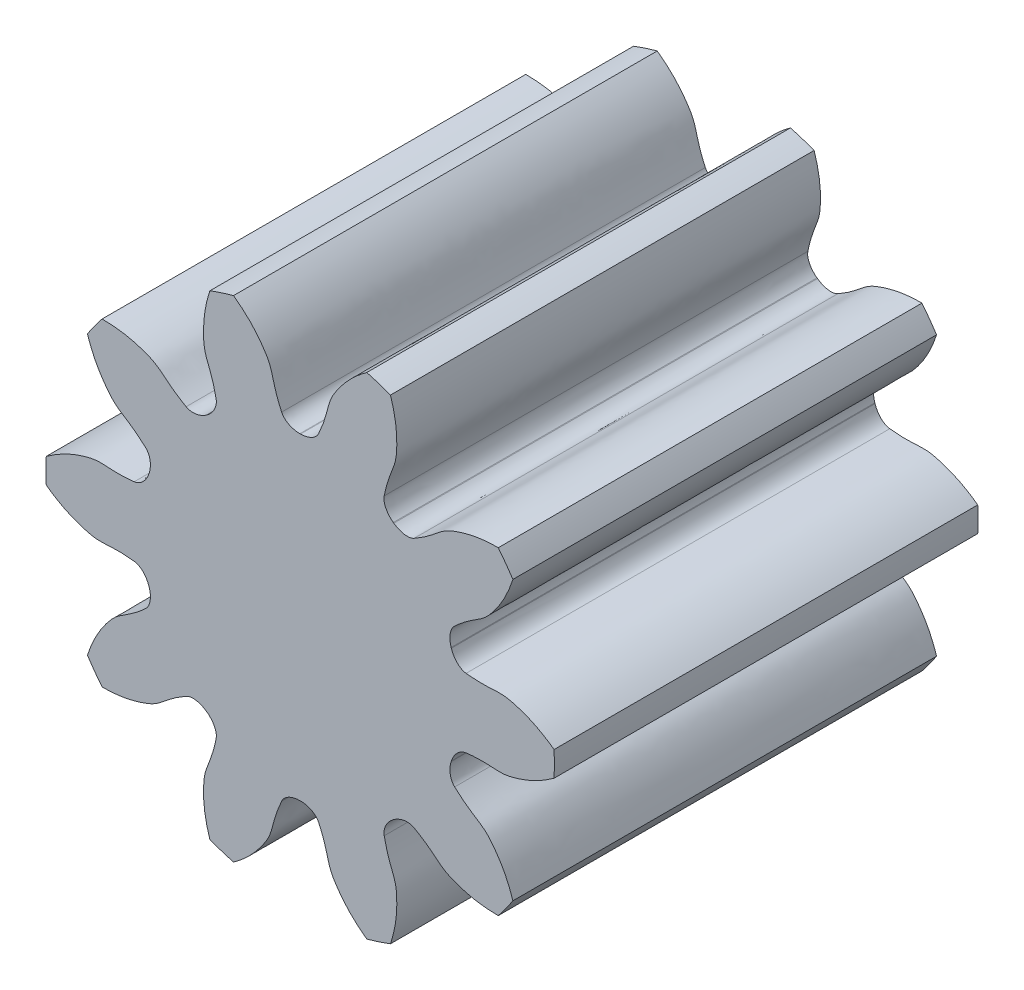
SolidWorks part; units mm, degrees
ref_plane "Plan de face" through (0, 0, 0) normal (0, 0, 1) x (1, 0, 0)
ref_plane "Plan de dessus" through (0, 0, 0) normal (0, 1, 0) x (1, 0, 0)
ref_plane "Plan de droite" through (0, 0, 0) normal (1, 0, 0) x (0, 0, -1)
sketch "Esquisse1" plane through (0, 0, 0) normal (0, 0, 1) x (1, 0, 0)
  circle A0 centre (0, 0) radius 2.4
  dimension "D1" = 4.8
extrude "Boss.-Extru.1" add sketch "Esquisse1" along normal blind 4
sketch "Dépose" plane through (-0.0454, -0.0909, 4) normal (0, 0, 1) x (1, 0, 0)
  line L0 (0.0454, 0.0909) -> (0.0454, 2.4909) construction
  circle A0 centre (0.0454, 0.0909) radius 2.4
  circle A1 centre (0.0454, 0.0909) radius 2.4 construction
  dimension "(d arbre)" = 4.8
sketch "Dimensions" plane through (-0.0454, -2.6509, 4) normal (0, 0, 1) x (1, 0, 0)
  line L0 (0.0454, 2.6509) -> (2.4454, 2.6509) construction
  line L1 (0.0454, 2.6509) -> (0.0454, 12.6509) construction
  line L2 (0.0454, 5.0509) -> (0.0454, 5.4509) construction
  line L3 (0.0454, 5.4509) -> (0.0454, 6.4509) construction
  line L4 (0.0454, 2.6509) -> (0.0454, 5.0509) construction
  line L5 (0.0454, 2.6509) -> (0.9851, 2.3088) construction
  line L6 (0.9851, 2.3088) -> (1.3387, 1.9553) construction
  line L7 (1.3387, 1.9553) -> (1.6922, 1.6017) construction
  line L8 (1.6922, 1.6017) -> (1.6993, 1.5947) construction
  line L9 (1.6993, 1.5947) -> (2.3357, 0.9583) construction
  line L10 (0.0454, 2.6509) -> (0.0454, 5.0509) construction
  line L11 (0.0454, 2.6509) -> (-0.9546, 2.6509) construction
  circle A0 centre (0.0454, 2.6509) radius 2.4 construction
  circle A1 centre (0.0454, 2.6509) radius 2.4
  circle A3 centre (0.0454, 5.2509) radius 0.2 construction
  circle A4 centre (0.0454, 2.6509) radius 2.4 construction
  dimension "(d tête)" = 4.8
  dimension "Z nb de dents" = 10
  dimension "module" = 0.4
  dimension "déport X+1" = 1
  dimension "A° de pression" = 20
  dimension "coef courbure flanc" = 1
  dimension "coef courbure raccord flanc" = 0.5
  dimension "coef courbure raccord fond" = 0.5
  dimension "coef fond/creux" = 0.01
  dimension "coef décalage bas-flanc" = 0.9
  dimension "A° tangence bas-flanc" = 25
  dimension "Reconstructions" = 1
ref_plane "Normal" through (0, 0, 4) normal (0, 0, 1) x (1, 0, 0)
sketch "Profil dent" plane through (0, 0, 4) normal (0, 0, 1) x (1, 0, 0)
  line L0 (0, 0) -> (0, 2) construction
  line L1 (-0.3129, 1.9754) -> (-0.9111, 1.6437) construction
  line L2 (-0.1748, 1.5904) -> (-0.1748, 1.8712) construction
  line L3 (0.7979, -0.4955) -> (-1.1474, 3.6763) construction
  line L7 (0, 0) -> (0, 10) construction
  line L8 (-0.629, 2.3161) -> (-1.5137, 1.1139) construction
  line L9 (0, 0) -> (-0.4458, 2.1544) construction
  line L10 (-0.4458, 2.1544) -> (-1.282, 1.3742) construction
  line L11 (-0.3129, 1.9754) -> (-0.9111, 1.6437) construction
  line L14 (0, 0) -> (-0.1748, 1.5904) construction
  line L16 (0, 0) -> (-0.6498, 2.3311) construction
  line L17 (-0.6498, 2.3311) -> (-1.5324, 1.088) construction
  circle A0 centre (0, 0) radius 2 construction
  circle A1 centre (0, 0) radius 1.8794 construction
  circle A2 centre (0, 0) radius 2 construction
  arc A3 (-0.9111, 1.6437) -> (-0.2663, 1.8604) centre (0, 0) cw construction
  arc A4 (0, 2) -> (-0.3129, 1.9754) centre (0, 0) ccw construction
  arc A5 (0.0031, 1.5) -> (-0.0031, 1.5) centre (0, 0) ccw
  arc A8 (0.6498, 2.3311) -> (-0.6498, 2.3311) centre (0, 0) ccw
  circle A9 centre (0, 0) radius 2.4 construction
  circle A10 centre (0, 0) radius 2.4 construction
  spline S0 degree 3 poles (-0.6498, 2.3311) (-0.5772, 2.2793) (-0.4569, 2.1825) (-0.3071, 1.9796) (-0.2624, 1.8624) (-0.2311, 1.7113) (-0.1748, 1.5904) knots 0 0 0 0 0.314464 0.566482 0.749018 1 1 1 1
  spline S1 degree 3 poles (0.6498, 2.3311) (0.5772, 2.2793) (0.4569, 2.1825) (0.3071, 1.9796) (0.2624, 1.8624) (0.2311, 1.7113) (0.1748, 1.5904) knots 0 0 0 0 0.314464 0.566482 0.749018 1 1 1 1
  spline S2 degree 3 poles (-0.1748, 1.5904) (-0.1466, 1.53) (-0.0698, 1.4999) (-0.0031, 1.5) knots 0 0 0 0 1 1 1 1
  spline S3 degree 3 poles (0.1748, 1.5904) (0.1466, 1.53) (0.0698, 1.4999) (0.0031, 1.5) knots 0 0 0 0 1 1 1 1
  dimension "Rb" = 1.8794
  dimension "Rt" = 2
  dimension "Rp" = 2
  dimension "Rf" = 1.5
  dimension "p" = 0.4
  dimension "p10" = 0.2
  dimension "p11" = 0.2
  dimension "Tref" = 0.684
  dimension "t1" = 1.4926
  dimension "r2" = 2.2
  dimension "t2" = 1.1436
  dimension "tt" = 0.684
  dimension "t0" = 1.5246
  dimension "r0" = 2.42
  dimension "r4" = 1.6
  dimension "decfond" = 0.0915
  dimension "A° bas-flanc" = 25
  dimension "Aref" = 0.684
  dimension "a1" = 1.4926
  dimension "a2" = 1.1436
  dimension "at" = 0.684
  dimension "a0" = 1.5246
  dimension "e/2" = 0.3142
  dimension "fond/creux" = 0.0063
extrude "Creux de dent" cut sketch "Profil dent" against normal blind 4
ref_axis "Axe denture" through (0, 0, -46) along (0, 0, 1)
pattern_circular "Denture" count 10 over 360 about axis through (0, 0, -46) along (0, 0, 1) of "Creux de dent"
other "Denture droite - Z petit<1>"
equation "\"Rp@Profil dent\" = (\"module@Dimensions\" * \"Z nb de dents@Dimensions\")/2"
equation "\"Rt@Profil dent\" = \"Rp@Profil dent\"+(\"déport X+1@Dimensions\"-1)*\"module@Dimensions\""
equation "\"Rb@Profil dent\" = \"Rp@Profil dent\" *cos(\"A° de pression@Dimensions\")                   ' *pi/180)"
equation "\"Aref@Profil dent\" = \"Tref@Profil dent\""
equation "\"e/2@Profil dent\" = \"module@Dimensions\"*((pi/4)-((\"déport X+1@Dimensions\"-1) *tan(\"A° de pression@Dimensions\")))              ' *pi/180)))"
equation "\"r0@Profil dent\" = \"Rt@Profil dent\" + 1.05*\"module@Dimensions\""
equation "\"a0@Profil dent\" = \"t0@Profil dent\""
equation "\"(d tête)@Dimensions\" = (\"Rt@Profil dent\" + \"module@Dimensions\")*2"
equation "\"a1@Profil dent\" = \"t1@Profil dent\""
equation "\"r2@Profil dent\" =\"Rt@Profil dent\" + 0.5*\"module@Dimensions\""
equation "\"a2@Profil dent\" = \"t2@Profil dent\""
equation "\"at@Profil dent\" = \"tt@Profil dent\""
equation "\"r4@Profil dent\" = \"Rt@Profil dent\" -\"module@Dimensions\""
equation "\"decfond@Profil dent\" = (\"Rb@Profil dent\" - \"r4@Profil dent\")* tan( \"A° de pression@Dimensions\" )*\"coef décalage bas-flanc@Dimensions\""
equation "\"Rf@Profil dent\" = \"Rt@Profil dent\" -1.25*\"module@Dimensions\" "
equation "\"A° bas-flanc@Profil dent\" = \"A° tangence bas-flanc@Dimensions\""
equation "\"p@Profil dent\"=\"module@Dimensions\"*\"coef courbure flanc@Dimensions\""
equation "\"p10@Profil dent\"=\"coef courbure raccord flanc@Dimensions\"*\"module@Dimensions\""
equation "\"p11@Profil dent\"=\"coef courbure raccord fond@Dimensions\"*\"module@Dimensions\""
equation "\"fond/creux@Profil dent\"=\"coef fond/creux@Dimensions\"*\"e/2@Profil dent\"*2"
equation "\"Z@Denture\" = \"Z nb de dents@Dimensions\""
